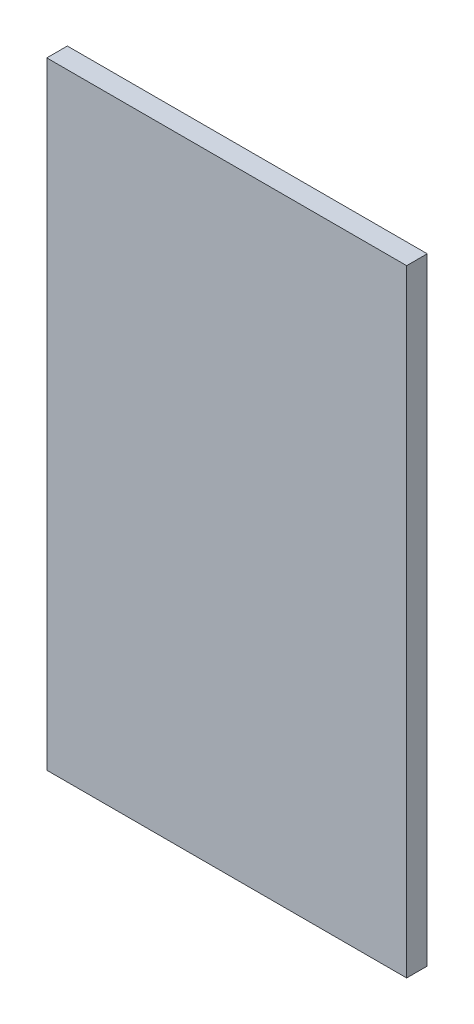
SolidWorks part; units mm, degrees
ref_plane "Front Plane" through (0, 0, 0) normal (1, 0, 0) x (0, 1, 0)
ref_plane "Top Plane" through (0, 0, 0) normal (0, 0, 1) x (0, 1, 0)
ref_plane "Right Plane" through (0, 0, 0) normal (0, 1, 0) x (-1, 0, 0)
sketch "Sketch1" plane through (0, 0, 0) normal (0, 0, 1) x (0, 1, 0)
  line L1 (-150, -87.5) -> (150, -87.5)
  line L2 (-150, -87.5) -> (-150, 87.5)
  line L3 (-150, 87.5) -> (150, 87.5)
  line L4 (150, -87.5) -> (150, 87.5)
  line L5 (-150, -87.5) -> (150, 87.5) construction
  line L6 (-150, 87.5) -> (150, -87.5) construction
  point P0 (0, 0)
  dimension "D1" = 300
  dimension "D2" = 175
extrude "Boss-Extrude1" add sketch "Sketch1" along normal blind 10
